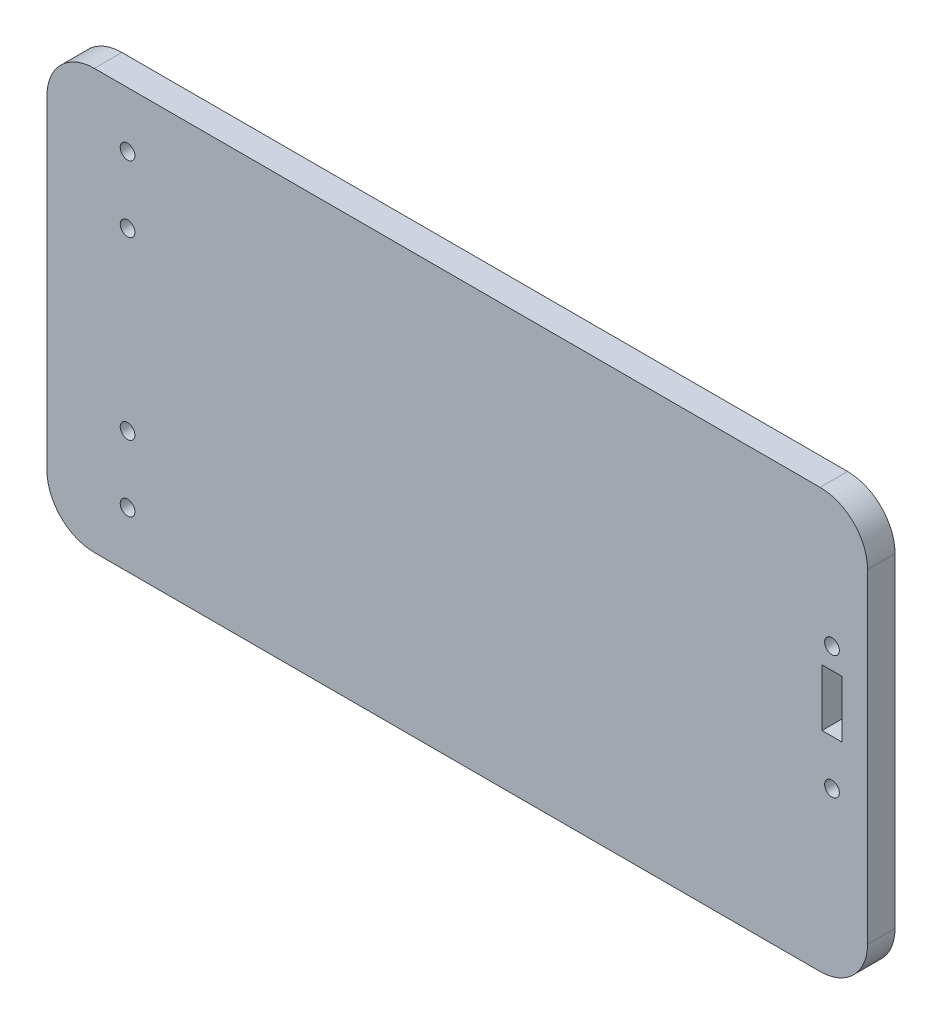
SolidWorks part; units mm, degrees
material "Acrylic (Medium-high impact)"
ref_plane "Front" through (0, 0, 0) normal (0, 0, 1) x (1, 0, 0)
ref_plane "Top" through (0, 0, 0) normal (0, 1, 0) x (1, 0, 0)
ref_plane "Right" through (0, 0, 0) normal (1, 0, 0) x (0, 0, -1)
sketch "Sketch2" plane through (0, 0, 0) normal (0, 0, 1) x (1, 0, 0)
  line L4 (163, 44.2) -> (10, 44.2)
  line L5 (0, 34.2) -> (0, -34.2)
  line L6 (163, -44.2) -> (10, -44.2)
  line L7 (173, 34.2) -> (173, -34.2)
  arc A4 (10, 44.2) -> (0, 34.2) centre (10, 34.2) ccw
  arc A5 (0, -34.2) -> (10, -44.2) centre (10, -34.2) ccw
  arc A6 (163, -44.2) -> (173, -34.2) centre (163, -34.2) ccw
  arc A7 (173, 34.2) -> (163, 44.2) centre (163, 34.2) ccw
  dimension "D3" = 10
  dimension "D1" = 173
  dimension "D2" = 88.4
extrude "Boss-Extrude1" add sketch "Sketch2" along normal blind 5.8
sketch "Sketch3" plane through (0, 0, 5.8) normal (0, 0, 1) x (1, 0, 0)
  line L0 (0, 34.2) -> (0, -34.2) construction
  line L1 (167.6, 0) -> (163.4, 0)
  line L2 (167.6, 0) -> (167.6, 12)
  line L3 (167.6, 12) -> (163.4, 12)
  line L4 (163.4, 0) -> (163.4, 12)
  point P7 (165.5, 12)
  dimension "D1" = 4.2
  dimension "D2" = 12
  dimension "D3" = 165.5
extrude "Cut-Extrude1" cut sketch "Sketch3" against normal blind 6.35
sketch "Sketch4" plane through (0, 0, 5.8) normal (0, 0, 1) x (1, 0, 0)
  line L0 (0, 0) -> (173, 0) construction
  line L1 (0, 34.2) -> (0, -34.2) construction
  line L2 (173, -34.2) -> (173, 34.2) construction
  line L3 (17, 32.5) -> (17, 18.5) construction
  line L4 (17, -32.5) -> (17, -18.5) construction
  circle A0 centre (17, 32.5) radius 1.55
  circle A1 centre (17, 18.5) radius 1.55
  circle A2 centre (17, -18.5) radius 1.55
  circle A3 centre (17, -32.5) radius 1.55
  point P14 (17, 25.5)
  dimension "D1" = 3.1
  dimension "D2" = 17
  dimension "D3" = 25.5
  dimension "D4" = 14
extrude "Cut-Extrude2" cut sketch "Sketch4" against normal through all
sketch "Sketch5" plane through (0, 0, 5.8) normal (0, 0, 1) x (1, 0, 0)
  line L0 (167.6, 12) -> (163.4, 12) construction
  line L1 (163.4, 0) -> (167.6, 0) construction
  circle A0 centre (165.5, 16.45) radius 1.55
  circle A1 centre (165.5, -9.55) radius 1.55
  point P9 (165.5, 12)
  dimension "D1" = 3.1
  dimension "D2" = 4.45
  dimension "D3" = 9.55
extrude "Cut-Extrude3" cut sketch "Sketch5" against normal through all
